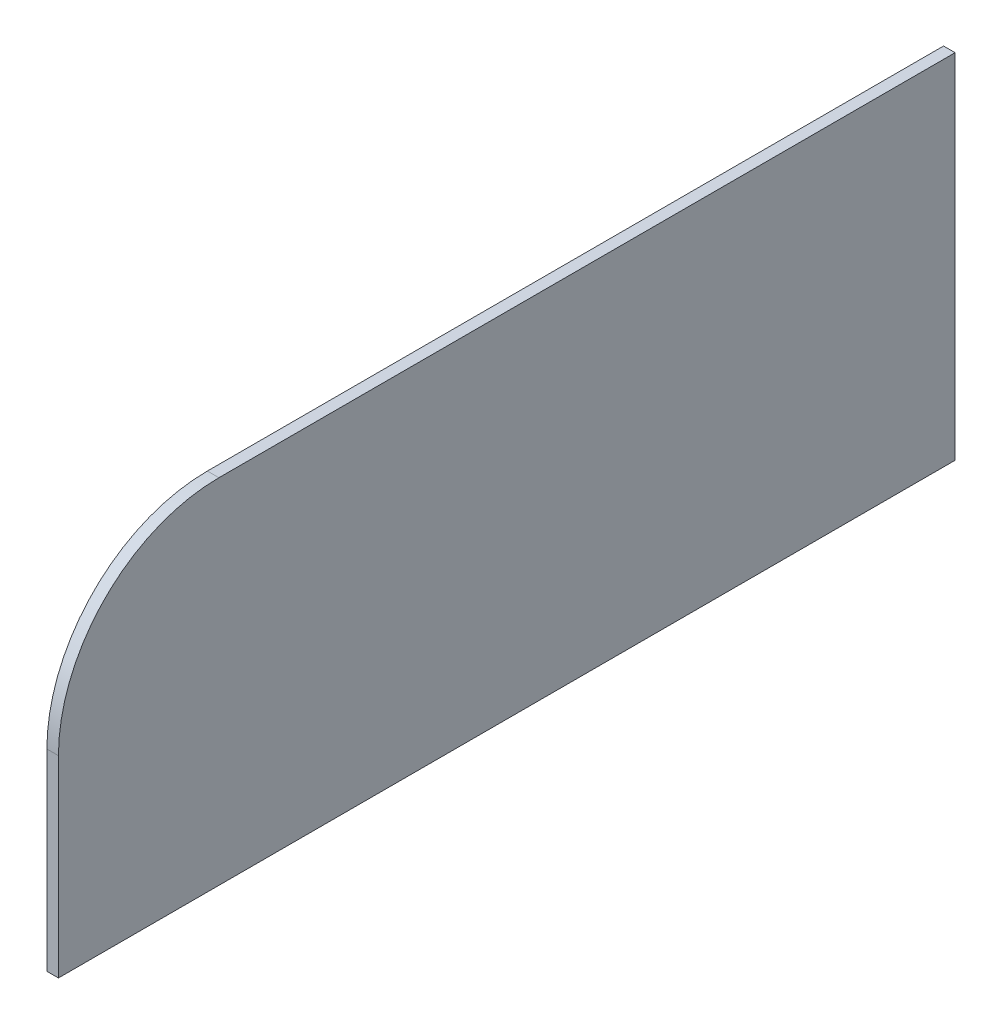
SolidWorks part; units mm, degrees
ref_plane "Front Plane" through (0, 0, 0) normal (0, 0, 1) x (1, 0, 0)
ref_plane "Top Plane" through (0, 0, 0) normal (0, 1, 0) x (1, 0, 0)
ref_plane "Right Plane" through (0, 0, 0) normal (1, 0, 0) x (0, 0, -1)
sketch "Sketch1" plane through (0, 0, 0) normal (1, 0, 0) x (0, 0, -1)
  line L1 (1129.3921, -492.2196) -> (-267.6079, -492.2196)
  line L2 (1129.3921, -492.2196) -> (1129.3921, 57.7804)
  line L3 (1129.3921, 57.7804) -> (-17.6079, 57.7804)
  line L4 (-267.6079, -492.2196) -> (-267.6079, -192.2196)
  line L5 (1129.3921, -492.2196) -> (-267.6079, 57.7804) construction
  line L6 (1129.3921, 57.7804) -> (-267.6079, -492.2196) construction
  arc A0 (-267.6079, -192.2196) -> (-17.6079, 57.7804) centre (-17.6079, -192.2196) cw
  point P0 (430.8921, -217.2196)
  dimension "D3" = 250
  dimension "D1" = 1397
  dimension "D2" = 550
extrude "Boss-Extrude1" add sketch "Sketch1" along normal blind 18
equation "\"H_POLKI\"=550"
equation "\"D2@Sketch1\"=\"H_POLKI\""
equation "\"DSP_WIDTH\"=18"
equation "\"D1@Boss-Extrude1\"=\"DSP_WIDTH\""
